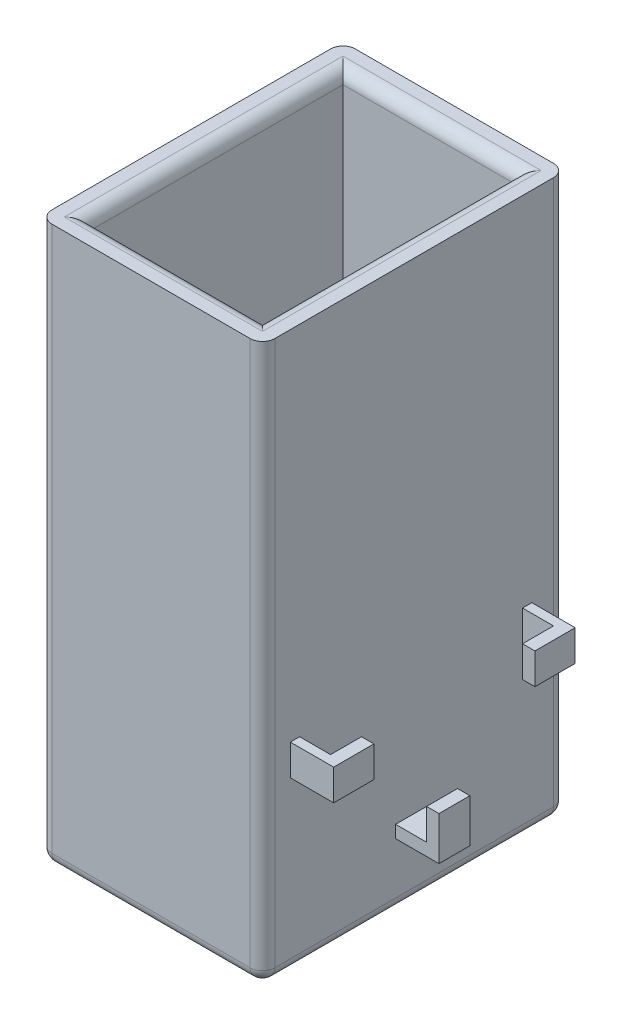
SolidWorks part; units mm, degrees
ref_plane "Front Plane" through (0, 0, 0) normal (0, 0, 1) x (1, 0, 0)
ref_plane "Top Plane" through (0, 0, 0) normal (0, 1, 0) x (1, 0, 0)
ref_plane "Right Plane" through (0, 0, 0) normal (1, 0, 0) x (0, 0, -1)
sketch "Sketch1" plane through (0, 0, 0) normal (0, 1, 0) x (1, 0, 0)
  line L1 (-14.8235, 20.4278) -> (21.1765, 20.4278)
  line L2 (-14.8235, 20.4278) -> (-14.8235, -28.5722)
  line L3 (-14.8235, -28.5722) -> (21.1765, -28.5722)
  line L4 (21.1765, 20.4278) -> (21.1765, -28.5722)
  point P4 (7.6765, 0.4278)
  dimension "D1" = 49
  dimension "D2" = 36
extrude "Boss-Extrude2" add sketch "Sketch1" along normal blind 90
shell "Shell3" thickness 4
fillet "Fillet1" radius 2 1 edges at (-14.8235, 45, -20.4278)
fillet "Fillet2" radius 2 1 edges at (21.1765, 45, -20.4278)
fillet "Fillet3" radius 2 1 edges at (21.1765, 45, 28.5722)
fillet "Fillet4" radius 2 1 edges at (-14.8235, 45, 28.5722)
fillet "Fillet5" radius 2 8 edges at (-14.8235, 0, 4.0722) (-14.2377, 0, -19.842) (3.1765, 0, -20.4278) (20.5907, 0, -19.842) (21.1765, 0, 4.0722) (20.5907, 0, 27.9864) (3.1765, 0, 28.5722) (-14.2377, 0, 27.9864)
ref_plane "Plane1" through (21.1765, 0, 0) normal (1, 0, 0) x (0, 0, -1)
sketch "Sketch7" plane through (21.1765, 0, 0) normal (1, 0, 0) x (0, 0, -1)
  line L11 (-24.0722, 32.3057) -> (-22.5722, 32.3057)
  line L12 (-24.0722, 32.3057) -> (-24.0722, 27.3057)
  line L13 (-24.0722, 27.3057) -> (-22.5722, 27.3057)
  line L14 (-22.5722, 32.3057) -> (-22.5722, 27.3057)
  line L16 (14.9278, 32.3057) -> (13.4278, 32.3057)
  line L17 (14.9278, 32.3057) -> (14.9278, 27.3057)
  line L18 (14.9278, 27.3057) -> (13.4278, 27.3057)
  line L19 (13.4278, 32.3057) -> (13.4278, 27.3057)
  line L20 (-2.0722, 12.3057) -> (-7.0722, 12.3057)
  line L21 (-2.0722, 12.3057) -> (-2.0722, 10.3057)
  line L22 (-2.0722, 10.3057) -> (-7.0722, 10.3057)
  line L23 (-7.0722, 12.3057) -> (-7.0722, 10.3057)
  point P8 (-23.0722, 29.8057)
  point P13 (13.9278, 29.8057)
  point P18 (-4.5722, 11.3057)
  dimension "D1" = 1.5
extrude "Boss-Extrude3" add sketch "Sketch7" along normal blind 7
ref_plane "Plane2" through (0, 0, 22.5722) normal (0, 0, -1) x (-1, 0, 0)
ref_plane "Plane3" through (0, 0, -13.4278) normal (0, 0, 1) x (1, 0, 0)
ref_plane "Plane5" through (0, 12.3057, 0) normal (0, 1, 0) x (1, 0, 0)
sketch "Sketch8" plane through (0, 0, 22.5722) normal (0, 0, -1) x (-1, 0, 0)
  line L0 (-28.1765, 27.3057) -> (-21.1765, 27.3057) construction
  line L1 (-28.1765, 32.3057) -> (-26.1765, 32.3057)
  line L2 (-28.1765, 32.3057) -> (-28.1765, 27.3057)
  line L3 (-28.1765, 27.3057) -> (-26.1765, 27.3057)
  line L4 (-26.1765, 32.3057) -> (-26.1765, 27.3057)
  dimension "D1" = 2
extrude "Boss-Extrude4" add sketch "Sketch8" along normal blind 5
sketch "Sketch9" plane through (0, 0, -13.4278) normal (0, 0, 1) x (1, 0, 0)
  line L0 (28.1765, 27.3057) -> (21.1765, 27.3057) construction
  line L1 (28.1765, 32.3057) -> (26.1765, 32.3057)
  line L2 (28.1765, 32.3057) -> (28.1765, 27.3057)
  line L3 (28.1765, 27.3057) -> (26.1765, 27.3057)
  line L4 (26.1765, 32.3057) -> (26.1765, 27.3057)
  dimension "D1" = 2
extrude "Boss-Extrude5" add sketch "Sketch9" along normal blind 5
sketch "Sketch10" plane through (0, 12.3057, 0) normal (0, 1, 0) x (1, 0, 0)
  line L0 (28.1765, -2.0722) -> (21.1765, -2.0722) construction
  line L1 (28.1765, -7.0722) -> (26.1765, -7.0722)
  line L2 (28.1765, -7.0722) -> (28.1765, -2.0722)
  line L3 (28.1765, -2.0722) -> (26.1765, -2.0722)
  line L4 (26.1765, -7.0722) -> (26.1765, -2.0722)
  dimension "D1" = 2
extrude "Boss-Extrude6" add sketch "Sketch10" along normal blind 5
fillet "Fillet7" radius 2 1 edges at (17.1765, 90, 4.0722)
fillet "Fillet8" radius 2 2 edges at (17.7623, 89.4142, -16.4278) (4.1765, 90, -16.4278)
fillet "Fillet9" radius 2 2 edges at (-10.8235, 90, 3.0722) (-10.8235, 89.4142, -17.0136)
fillet "Fillet10" radius 2 3 edges at (17.7623, 89.4142, 24.5722) (3.1765, 90, 24.5722) (-11.4093, 89.4142, 24.5722)
